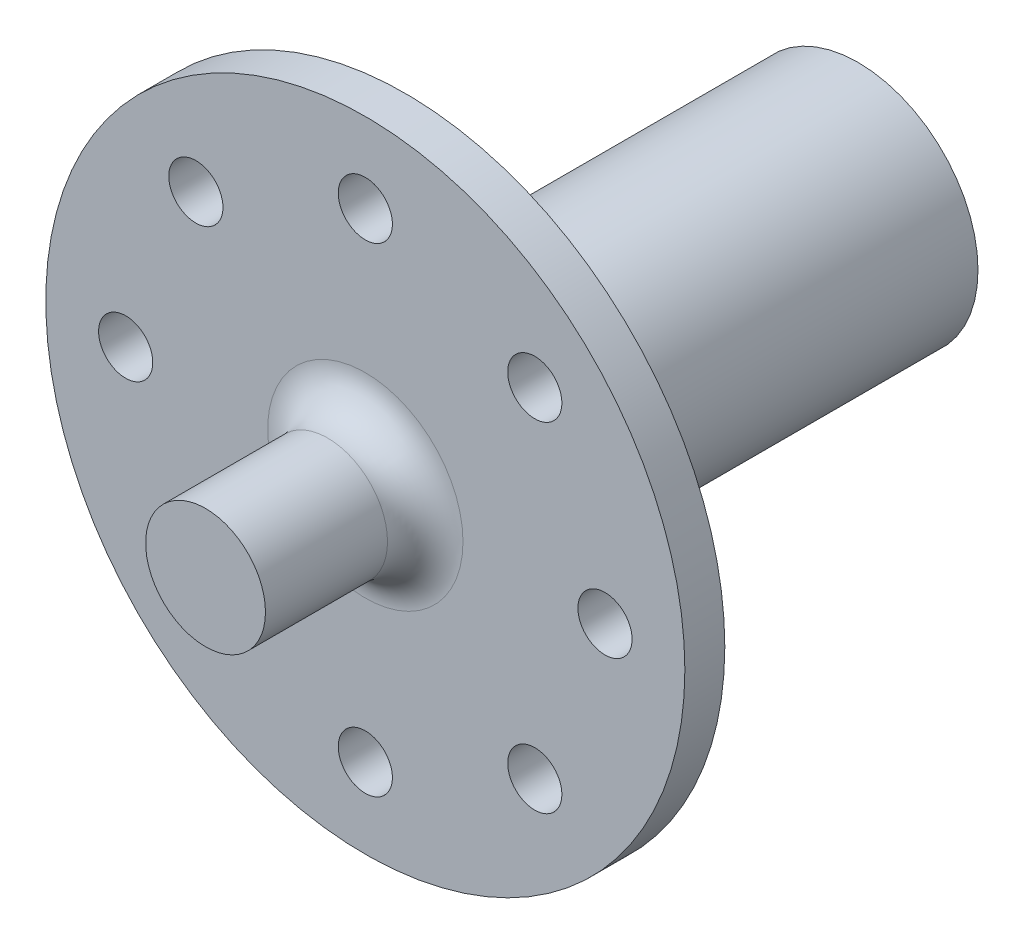
SolidWorks part; units mm, degrees
ref_plane "Front Plane" through (0, 0, 0) normal (0, 0, 1) x (1, 0, 0)
ref_plane "Top Plane" through (0, 0, 0) normal (0, 1, 0) x (1, 0, 0)
ref_plane "Right Plane" through (0, 0, 0) normal (1, 0, 0) x (0, 0, -1)
sketch "Sketch1" plane through (0, 0, 0) normal (0, 0, 1) x (1, 0, 0)
  line L0 (-1.5, 5.2) -> (1.5, 5.2)
  line L1 (-1.5, 5.2) -> (-1.5, 3.7081)
  line L2 (1.5, 5.2) -> (1.5, 3.7081)
  arc A0 (-1.5, 3.7081) -> (1.5, 3.7081) centre (0, 0) ccw
  circle A1 centre (0, 0) radius 9.525
  point P1 (0, -4)
  point P5 (0, 5.2)
  dimension "D1" = 8
  dimension "D4" = 19.05
  dimension "D2" = 3
  dimension "D3" = 9.2
extrude "Boss-Extrude1" add sketch "Sketch1" along normal blind 36
sketch "Sketch2" plane through (0, 0, 36) normal (0, 0, 1) x (1, 0, 0)
  circle A0 centre (0, 0) radius 25.4
  dimension "D1" = 50.8
extrude "Boss-Extrude2" add sketch "Sketch2" along normal blind 3.175
sketch "Sketch3" plane through (0, 0, 39.175) normal (0, 0, 1) x (1, 0, 0)
  circle A0 centre (0, 0) radius 4.7625
  dimension "D1" = 9.525
extrude "Boss-Extrude3" add sketch "Sketch3" along normal blind 12.7
sketch "Sketch4" plane through (0, 0, 39.175) normal (0, 0, 1) x (1, 0, 0)
  line L0 (0, 0) -> (0, 25.4) construction
  line L1 (-20.1972, -20.1972) -> (20.1972, 20.1972) construction
  line L2 (-19.837, 19.837) -> (19.837, -19.837) construction
  line L3 (0, 0) -> (35.2986, 0) construction
  circle A0 centre (0, 0) radius 19.05 construction
  circle A1 centre (0, 0) radius 25.4 construction
  circle A2 centre (0, 19.05) radius 2.1526
  circle A3 centre (13.4704, 13.4704) radius 2.1526
  circle A4 centre (19.05, 0) radius 2.1527
  circle A5 centre (13.4704, -13.4704) radius 2.1526
  circle A6 centre (-19.05, 0) radius 2.1527
  circle A7 centre (0, -19.05) radius 2.1526
  circle A8 centre (-13.4704, -13.4704) radius 2.1527
  circle A9 centre (-13.4704, 13.4704) radius 2.1526
  point P10 (0, 0)
  point P11 (-19.05, 0)
  point P14 (0, 0)
  point P16 (0, -19.05)
  point P17 (19.05, 0)
  point P19 (0, 19.05)
  dimension "D1" = 45
  dimension "D3" = 4.3053
  dimension "D4" = 38.1
  dimension "D2" = 45
extrude "Cut-Extrude1" cut sketch "Sketch4" against normal blind 19.05
fillet "Fillet1" radius 3 1 edges at (4.7625, 0, 39.175)
sketch "Sketch5" plane through (0, 0, 36) normal (0, 0, -1) x (-1, 0, 0)
  line L0 (1.5, 5.2) -> (1.5, 3.7081) construction
  line L1 (-1.5, 5.2) -> (1.5, 5.2) construction
  line L2 (-1.5, 3.7081) -> (-1.5, 5.2) construction
  line L3 (1.5, 5.2) -> (1.5, 3.7081)
  line L4 (-1.5, 5.2) -> (1.5, 5.2)
  line L5 (-1.5, 3.7081) -> (-1.5, 5.2)
  line L6 (-1.5, 3.7081) -> (1.5, 3.7081)
extrude "Boss-Extrude4" add sketch "Sketch5" along normal offset from surface (10.6 mm away) 25.4 up to face at (9.525, 0, 0)
